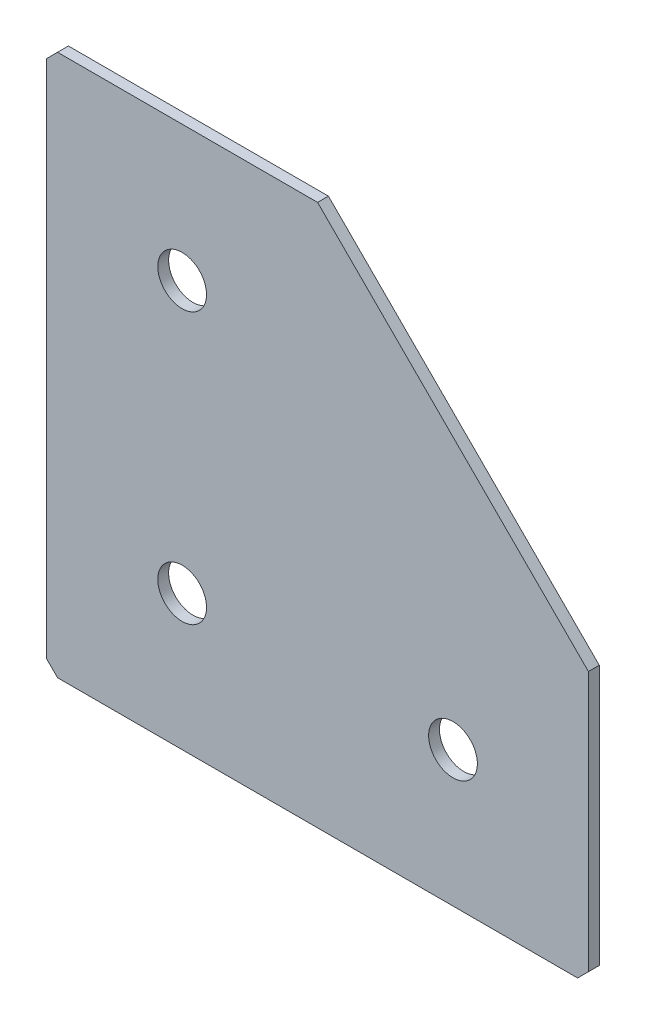
SolidWorks part; units mm, degrees
material "Простая углеродистая сталь"
ref_plane "Спереди(Плоскость XY)" through (0, 0, 0) normal (0, 0, 1) x (1, 0, 0)
ref_plane "Сверху(Плоскость XZ)" through (0, 0, 0) normal (0, 1, 0) x (1, 0, 0)
ref_plane "Справа(Плоскость ZY)" through (0, 0, 0) normal (1, 0, 0) x (0, 0, -1)
sketch "Эскиз1" plane through (0, 0, 0) normal (0, 0, -1) x (1, 0, 0)
  line L0 (0, 0) -> (0, 100)
  line L1 (0, 100) -> (100, 100)
  line L2 (100, 100) -> (100, 50)
  line L3 (100, 50) -> (50, 50) construction
  line L4 (50, 50) -> (50, 0) construction
  line L5 (50, 0) -> (0, 0)
  line L6 (100, 50) -> (50, 0)
  dimension "D1" = 100
  dimension "D2" = 50
  dimension "D3" = 50
  dimension "D4" = 50
extrude "Бобышка-Вытянуть1" add sketch "Эскиз1" along normal blind 2
hole_wizard "Отверстие с зазором M81" positions "Эскиз2" profile "Эскиз3" hole size "M8" standard "DIN" end condition through all
sketch "Эскиз2" plane through (0, 0, -2) normal (0, 0, -1) x (1, 0, 0)
  line L1 (0, 0) -> (50, 0) construction
  line L6 (0, 100) -> (0, 0) construction
  point P4 (25, 75)
  point P6 (25, 25)
  point P29 (75, 75)
  dimension "D1" = 50
  dimension "D2" = 50
  dimension "D4" = 25
  dimension "D5" = 25
sketch "Эскиз3" plane through (25, -75, -2) normal (1, 0, 0) x (0, 1, 0)
  line L0 (0, 0) -> (0, 2)
  line L1 (0, 2) -> (4.5, 2)
  line L2 (4.5, 2) -> (4.5, 0)
  line L5 (4.5, 0) -> (0, 0)
  line L11 (0, -6.35) -> (0, 107.95) construction
  dimension "Диаметр сквозного отверстия" = 9
  dimension "Глубина сквозного отверстия" = 2
chamfer "Фаска1" distance 2 angle 45 3 edges at (0, 0, -1) (100, -100, -1) (0, -100, -1)
